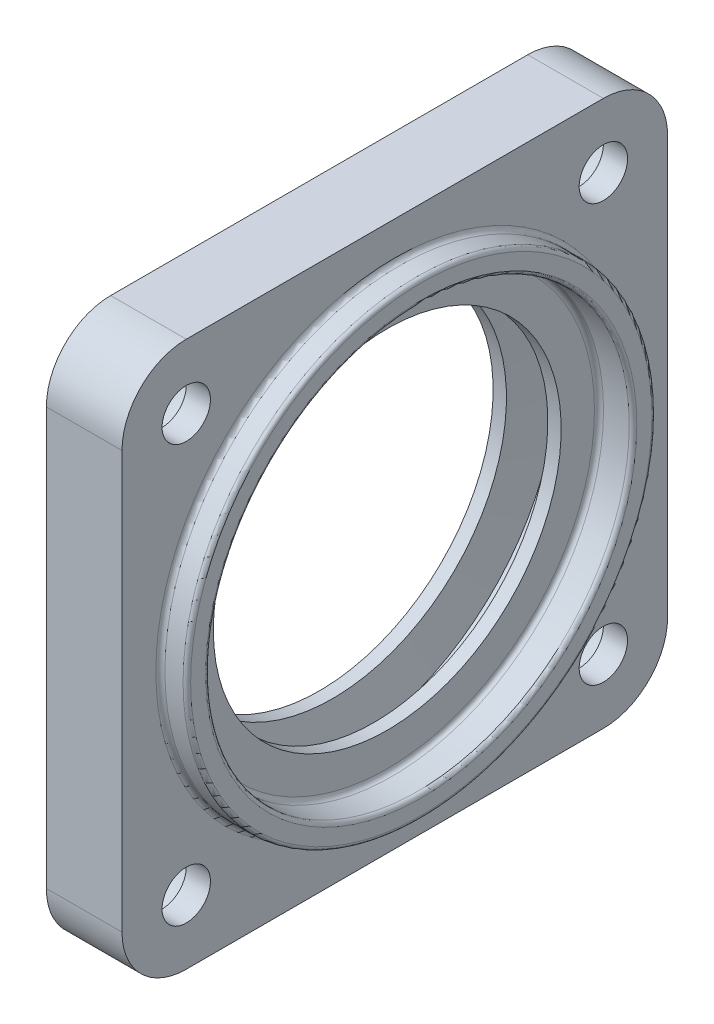
SolidWorks part; units mm, degrees
material "Сталь 3кп ГОСТ 535-88"
ref_plane "Спереди" through (0, 0, 0) normal (0, 0, 1) x (1, 0, 0)
ref_plane "Сверху" through (0, 0, 0) normal (0, 1, 0) x (1, 0, 0)
ref_plane "Слева" through (0, 0, 0) normal (1, 0, 0) x (0, 0, -1)
sketch "Эскиз1" plane through (0, 0, 0) normal (0, 0, 1) x (1, 0, 0)
  line L0 (0, 0) -> (65.0332, 0) construction
  line L1 (0, 0) -> (0, 29) construction
  line L2 (-4.5, 23) -> (-2.7367, 23)
  line L3 (-2.7367, 23) -> (-2, 29)
  line L4 (-2, 29) -> (2, 29)
  line L5 (2, 29) -> (2.7367, 23)
  line L6 (2.7367, 23) -> (4.5, 23)
  line L7 (4.5, 23) -> (4.5, 28)
  line L8 (4.5, 28) -> (10.5, 28)
  line L9 (10.5, 28) -> (10.5, 31)
  line L10 (10.5, 31) -> (5.5, 31)
  line L11 (5.5, 31) -> (5.5, 47.5)
  line L12 (5.5, 47.5) -> (-4.5, 47.5)
  line L13 (-4.5, 47.5) -> (-4.5, 23)
  dimension "D1" = 4
  dimension "D2" = 14
  dimension "D3" = 6
  dimension "D4" = 5
  dimension "D5" = 12.5
  dimension "D6" = 15
  dimension "D7" = 46
  dimension "D8" = 58
  dimension "D9" = 56
  dimension "D10" = 62
  dimension "D11" = 95
  dimension "D12" = 3
revolve "Повернуть1" add sketch "Эскиз1" angle 360 about L0
sketch "Эскиз2" plane through (-4.5, 0, 0) normal (-1, 0, 0) x (0, 0, 1)
  line L1 (-27.5772, -27.5772) -> (27.5772, -27.5772)
  line L2 (-27.5772, -27.5772) -> (-27.5772, 27.5772)
  line L3 (-27.5772, 27.5772) -> (27.5772, 27.5772)
  line L4 (27.5772, -27.5772) -> (27.5772, 27.5772)
  line L5 (-27.5772, -27.5772) -> (27.5772, 27.5772) construction
  line L6 (-27.5772, 27.5772) -> (27.5772, -27.5772) construction
  circle A0 centre (0, 0) radius 39
  dimension "D1" = 78
hole_wizard "Цековка для  болта с шестигранной головкой M61" positions "Трехмерный эскиз1" profile "Эскиз3" counterbore size "M6" standard "ГОСТ" end condition through all
sketch3d "Трехмерный эскиз1"
  point P0 (-4.5, 27.5772, -27.5772)
  point P3 (-4.5, 27.5772, 27.5772)
  point P6 (-4.5, -27.5772, 27.5772)
  point P9 (-4.5, -27.5772, -27.5772)
sketch "Эскиз3" plane through (-4.5, 27.5772, -27.5772) normal (0, 1, 0) x (0, 0, 1)
  line L0 (0, 0) -> (0, 15)
  line L1 (0, 15) -> (3.2, 15)
  line L3 (3.2, 15) -> (3.2, 6.8)
  line L4 (3.2, 6.8) -> (5.5, 6.8)
  line L5 (5.5, 6.8) -> (5.5, 0)
  line L7 (5.5, 0) -> (0, 0)
  line L11 (0, -6.35) -> (0, 107.95) construction
  dimension "Диаметр сквозного отверстия" = 6.4
  dimension "Глубина сквозного отверстия" = 15
  dimension "Диаметр цековки" = 11
  dimension "Глубина цековки" = 6.8
sketch "Эскиз4" plane through (-4.5, 0, 0) normal (-1, 0, 0) x (0, 0, 1)
  line L0 (-36.0772, 27.5772) -> (-36.0772, -27.5772)
  line L2 (-27.5772, -36.0772) -> (27.5772, -36.0772)
  line L4 (36.0772, -27.5772) -> (36.0772, 27.5772)
  line L6 (27.5772, 36.0772) -> (-27.5772, 36.0772)
  arc A0 (-27.5772, 36.0772) -> (-36.0772, 27.5772) centre (-27.5772, 27.5772) ccw
  arc A1 (36.0772, 27.5772) -> (27.5772, 36.0772) centre (27.5772, 27.5772) ccw
  circle A2 centre (0, 0) radius 47.5 construction
  arc A3 (27.5772, -36.0772) -> (36.0772, -27.5772) centre (27.5772, -27.5772) ccw
  arc A4 (-36.0772, -27.5772) -> (-27.5772, -36.0772) centre (-27.5772, -27.5772) ccw
  dimension "D1" = 17
extrude "Вытянуть1" cut sketch "Эскиз4" against normal through all flip side to cut
sketch "Эскиз5" plane through (10.5, 0, 0) normal (1, 0, 0) x (0, 0, -1)
  circle A1 centre (0, 0) radius 31
  circle A2 centre (0, 0) radius 31
  dimension "D1" = 0
extrude "Вытянуть2" cut sketch "Эскиз5" against normal blind 1.5
fillet "Скругление1" radius 0.6 1 edges at (5.5, 0, 31)
fillet "Скругление2" radius 0.5 2 edges at (9, 0, -28) (9, 0, -31)
fillet "Скругление3" radius 0.6 1 edges at (4.5, 0, 28)
